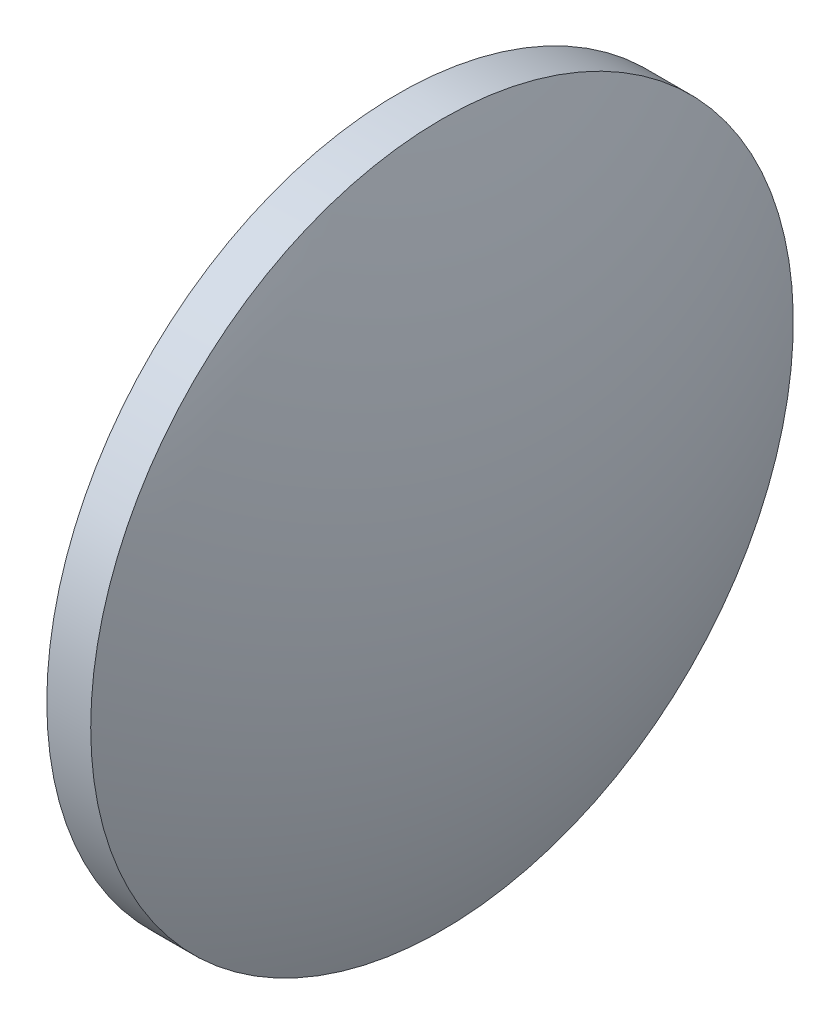
SolidWorks part; units mm, degrees
ref_plane "前视基准面" through (0, 0, 0) normal (0, 0, 1) x (1, 0, 0)
ref_plane "上视基准面" through (0, 0, 0) normal (0, 1, 0) x (1, 0, 0)
ref_plane "右视基准面" through (0, 0, 0) normal (1, 0, 0) x (0, 0, -1)
sketch "草图1" plane through (0, 0, 0) normal (0, 0, 1) x (1, 0, 0)
  line L0 (530.9568, 183.9812) -> (557.8483, 183.9812) construction
  line L1 (540.4633, 183.9812) -> (540.4633, 203.9812)
  line L2 (546.9933, 183.9812) -> (540.4633, 183.9812)
  line L5 (540.4633, 203.9812) -> (542.9633, 203.9812)
  arc A0 (546.9933, 183.9812) -> (542.9633, 203.9812) centre (495.3505, 183.9812) ccw
revolve "旋转1" add sketch "草图1" angle 360 about L0
